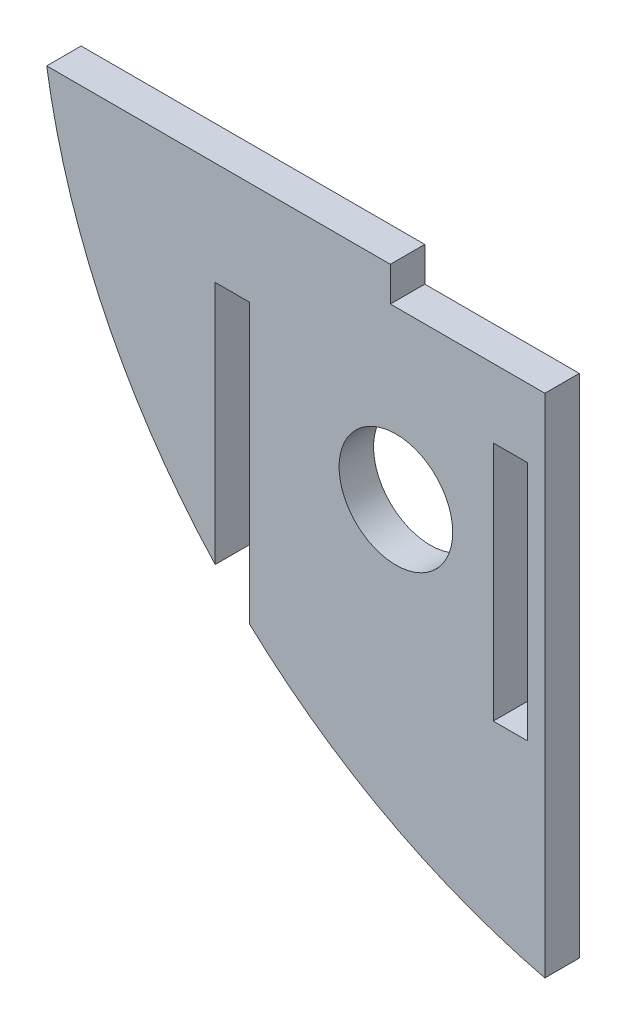
SolidWorks part; units mm, degrees
ref_plane "Front Plane" through (0, 0, 0) normal (0, 0, 1) x (1, 0, 0)
ref_plane "Top Plane" through (0, 0, 0) normal (0, 1, 0) x (1, 0, 0)
ref_plane "Right Plane" through (0, 0, 0) normal (1, 0, 0) x (0, 0, -1)
sketch "Sketch1" plane through (0, 0, 0) normal (0, 0, 1) x (1, 0, 0)
  line L0 (-19.2534, 9.7141) -> (-19.2534, -6.4891)
  line L2 (-5.097, -4.2859) -> (-5.097, 9.7141)
  line L3 (-19.2534, 9.7141) -> (-21.2534, 9.7141)
  line L4 (-11.0757, 13.7141) -> (-11.0757, 15.7141)
  line L5 (-11.0757, 13.7141) -> (-2.097, 13.7141)
  line L6 (-11.0757, 15.7141) -> (-31.0457, 15.7141)
  line L7 (-5.097, -4.2859) -> (-3.097, -4.2859)
  line L8 (-3.097, -4.2859) -> (-3.097, 9.7141)
  line L9 (-3.097, 9.7141) -> (-5.097, 9.7141)
  line L10 (-21.2534, 9.7141) -> (-21.2534, -4.4854)
  line L11 (-2.097, -15.7141) -> (-2.097, 13.7141)
  circle A0 centre (-10.7534, 4.0364) radius 3.3
  arc A1 (-31.0457, 15.7141) -> (-21.2534, -4.4854) centre (6.9377, 21.6543) ccw
  arc A2 (-19.2534, -6.4891) -> (-2.097, -15.7141) centre (6.9377, 21.6543) ccw
  dimension "D1" = 6.6
  dimension "D2" = 38.4451
  dimension "D3" = 6.9377
  dimension "D4" = 2.097
  dimension "D5" = 3.097
  dimension "D6" = 5.097
  dimension "D7" = 10.7534
  dimension "D8" = 19.2534
  dimension "D9" = 31.0457
  dimension "D10" = 4.0364
  dimension "D11" = 9.7141
  dimension "D12" = 13.7141
  dimension "D13" = 4.2859
extrude "Boss-Extrude1" add sketch "Sketch1" along normal blind 2
